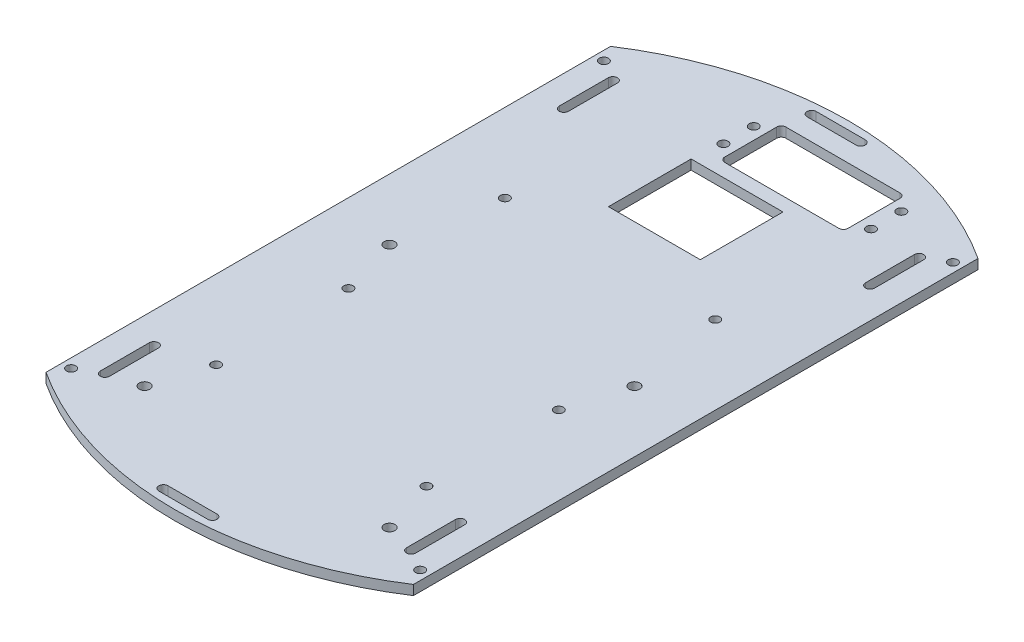
SolidWorks part; units mm, degrees
ref_plane "前视基准面" through (0, 0, 0) normal (0, 0, 1) x (1, 0, 0)
ref_plane "上视基准面" through (0, 0, 0) normal (0, 1, 0) x (1, 0, 0)
ref_plane "右视基准面" through (0, 0, 0) normal (1, 0, 0) x (0, 0, -1)
other "Configuration Table"
sketch "草图1" plane through (0, 0, 0) normal (0, 1, 0) x (1, 0, 0)
  line L0 (0, 0) -> (26.3372, 0) construction
  line L1 (0, 0) -> (0, 15.6752) construction
  line L4 (-60, 29.1954) -> (-60, -155.1954)
  line L6 (60, 29.1954) -> (60, -155.1954)
  line L9 (-8.55, 35) -> (28.75, 35)
  line L10 (-10.05, 33.5) -> (-10.05, 16.5)
  line L11 (-8.55, 15) -> (28.75, 15)
  line L12 (30.25, 33.5) -> (30.25, 16.5)
  line L15 (60, -63) -> (-143.5992, -63) construction
  line L22 (-8, 41.3595) -> (8, 41.3595)
  line L23 (-8, 44.3595) -> (8, 44.3595)
  line L24 (-8, -170.3595) -> (8, -170.3595)
  line L25 (-8, -167.3595) -> (8, -167.3595)
  line L26 (-48.5, 19.95) -> (-48.5, 3.95)
  line L27 (-51.5, 3.95) -> (-51.5, 19.95)
  line L28 (51.5, 3.95) -> (51.5, 19.95)
  line L29 (48.5, 19.95) -> (48.5, 3.95)
  line L30 (48.5, -145.95) -> (48.5, -129.95)
  line L31 (51.5, -129.95) -> (51.5, -145.95)
  line L32 (-51.5, -129.95) -> (-51.5, -145.95)
  line L33 (-48.5, -145.95) -> (-48.5, -129.95)
  line L35 (-15, 10.5) -> (15, 10.5)
  line L36 (-15, 10.5) -> (-15, -16.5)
  line L37 (-15, -16.5) -> (15, -16.5)
  line L38 (15, 10.5) -> (15, -16.5)
  line L39 (-15, 10.5) -> (15, -16.5) construction
  line L40 (-15, -16.5) -> (15, 10.5) construction
  circle A0 centre (-57, -150) radius 1.5
  circle A1 centre (57, -150) radius 1.5
  circle A2 centre (57, 24) radius 1.5
  circle A3 centre (-57, 24) radius 1.5
  arc A8 (-10.05, 16.5) -> (-8.55, 15) centre (-8.55, 16.5) ccw
  arc A9 (28.75, 15) -> (30.25, 16.5) centre (28.75, 16.5) ccw
  arc A10 (28.75, 35) -> (30.25, 33.5) centre (28.75, 33.5) cw
  arc A11 (-8.55, 35) -> (-10.05, 33.5) centre (-8.55, 33.5) ccw
  circle A14 centre (-14, 29.95) radius 1.5
  circle A15 centre (-14, 20.05) radius 1.5
  circle A16 centre (34.2, 29.95) radius 1.5
  circle A17 centre (34.2, 20.05) radius 1.5
  circle A18 centre (-40, -63) radius 1.75
  circle A19 centre (-40, -143) radius 1.75
  circle A20 centre (40, -143) radius 1.75
  circle A21 centre (40, -63) radius 1.75
  circle A26 centre (-34.35, -82.0749) radius 1.5
  circle A27 centre (-34.35, -125.2749) radius 1.5
  circle A28 centre (34.35, -125.2749) radius 1.5
  circle A29 centre (34.35, -82.0749) radius 1.5
  circle A30 centre (-34.35, -30.9745) radius 1.5
  circle A31 centre (34.35, -30.9745) radius 1.5
  arc A40 (-60, -155.1954) -> (60, -155.1954) centre (0, -63) ccw
  arc A41 (60, 29.1954) -> (-60, 29.1954) centre (0, -63) ccw
  arc A42 (-8, 44.3595) -> (-8, 41.3595) centre (-8, 42.8595) ccw
  arc A43 (8, 44.3595) -> (8, 41.3595) centre (8, 42.8595) cw
  arc A44 (-8, -170.3595) -> (-8, -167.3595) centre (-8, -168.8595) cw
  arc A45 (8, -170.3595) -> (8, -167.3595) centre (8, -168.8595) ccw
  arc A46 (-48.5, 19.95) -> (-51.5, 19.95) centre (-50, 19.95) ccw
  arc A47 (-51.5, 3.95) -> (-48.5, 3.95) centre (-50, 3.95) ccw
  arc A48 (48.5, 19.95) -> (51.5, 19.95) centre (50, 19.95) cw
  arc A49 (51.5, 3.95) -> (48.5, 3.95) centre (50, 3.95) cw
  arc A50 (51.5, -129.95) -> (48.5, -129.95) centre (50, -129.95) ccw
  arc A51 (48.5, -145.95) -> (51.5, -145.95) centre (50, -145.95) ccw
  arc A52 (-48.5, -145.95) -> (-51.5, -145.95) centre (-50, -145.95) cw
  arc A53 (-51.5, -129.95) -> (-48.5, -129.95) centre (-50, -129.95) cw
  point P4 (0, 0)
  point P14 (0, 0)
  point P34 (-10.05, 25)
  point P94 (0, -63)
  point P100 (0, -3)
  dimension "D3" = 3
  dimension "D5" = 3
  dimension "D9" = 1.5
  dimension "D11" = 3
  dimension "D16" = 9.9
  dimension "D19" = 3
  dimension "D17" = 3
  dimension "D23" = 3
  dimension "D24" = 3
  dimension "D25" = 3.5
  dimension "D29" = 3
  dimension "D32" = 27
  dimension "D34" = 220
  dimension "D14" = 3
  dimension "D2" = 20
  dimension "D4" = 3
  dimension "D6" = 16
  dimension "D7" = 40.3
  dimension "D8" = 30.25
  dimension "D10" = 3.95
  dimension "D12" = 35
  dimension "D13" = 120
  dimension "D15" = 60
  dimension "D18" = 16
  dimension "D20" = 50
  dimension "D21" = 4.95
  dimension "D22" = 3.95
  dimension "D26" = 40
  dimension "D27" = 80
  dimension "D28" = 30
  dimension "D30" = 43.2
  dimension "D31" = 34.35
  dimension "D33" = 60
extrude "凸台-拉伸1" add sketch "草图1" along normal blind 3.175
